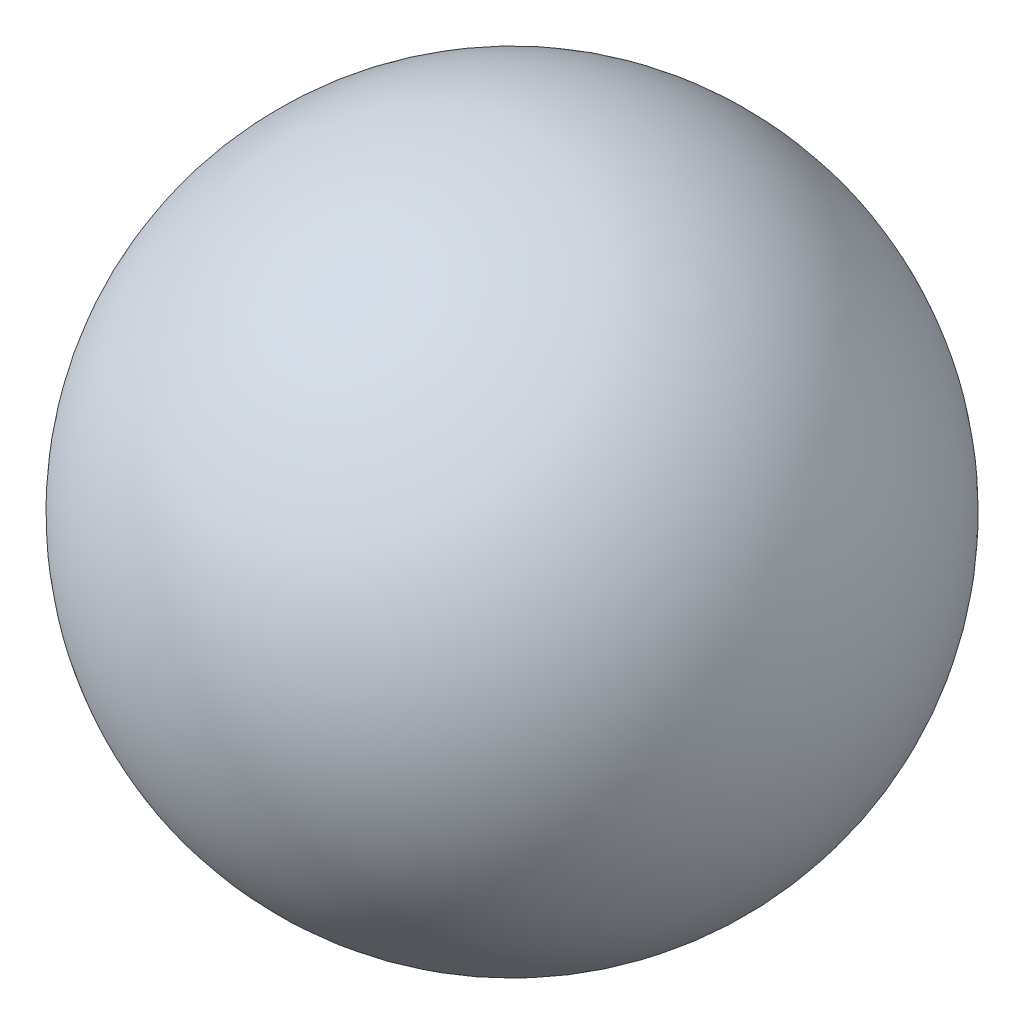
SolidWorks part; units mm, degrees
ref_plane "Front Plane" through (0, 0, 0) normal (0, 0, 1) x (1, 0, 0)
ref_plane "Top Plane" through (0, 0, 0) normal (0, 1, 0) x (1, 0, 0)
ref_plane "Right Plane" through (0, 0, 0) normal (1, 0, 0) x (0, 0, -1)
sketch "Sketch2" plane through (0, 0, 0) normal (0, 1, 0) x (1, 0, 0)
  line L0 (0, 0) -> (0, 60) construction
  line L1 (0, 0) -> (0, 60)
  arc A0 (0, 60) -> (0, 0) centre (0, 30) ccw
  dimension "D1" = 60
revolve "Revolve2" add sketch "Sketch2" angle 360 about L0
